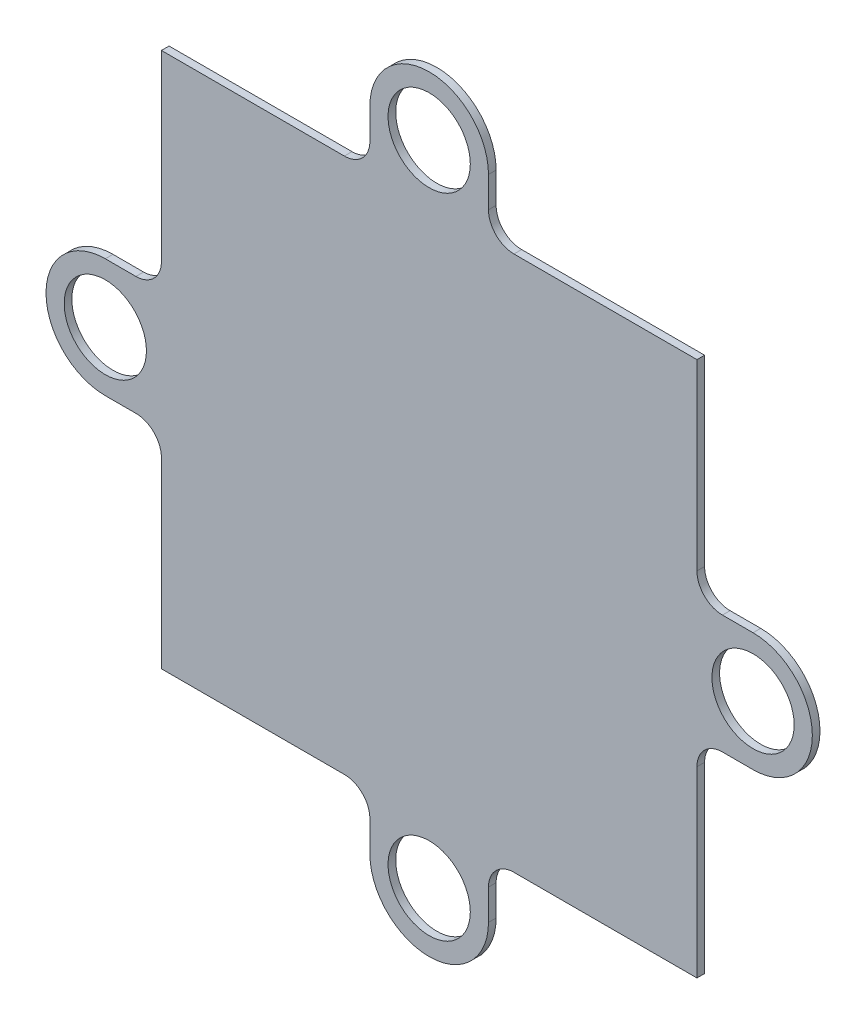
SolidWorks part; units mm, degrees
ref_plane "Front Plane" through (0, 0, 0) normal (0, 0, 1) x (1, 0, 0)
ref_plane "Top Plane" through (0, 0, 0) normal (0, 1, 0) x (1, 0, 0)
ref_plane "Right Plane" through (0, 0, 0) normal (1, 0, 0) x (0, 0, -1)
sketch "Sketch1" plane through (0, 0, 0) normal (0, 0, 1) x (1, 0, 0)
  line L0 (-4.65, 25.4) -> (-4.65, 23)
  line L1 (-21, -21) -> (-6.65, -21)
  line L2 (-21, -21) -> (-21, -6.65)
  line L3 (-21, 21) -> (-6.65, 21)
  line L4 (21, -21) -> (21, -6.65)
  line L5 (-21, -21) -> (21, 21) construction
  line L6 (-21, 21) -> (21, -21) construction
  line L7 (-6.65, 21) -> (-8.7591, 21)
  line L8 (4.65, 25.4) -> (4.65, 23)
  line L9 (6.65, 21) -> (7.1335, 21)
  line L10 (25.4, 4.65) -> (23, 4.65)
  line L11 (21, 6.65) -> (21, 8.7591)
  line L12 (25.4, -4.65) -> (23, -4.65)
  line L13 (21, -6.65) -> (21, -7.1335)
  line L14 (4.65, -25.4) -> (4.65, -23)
  line L15 (6.65, -21) -> (8.7591, -21)
  line L16 (-4.65, -25.4) -> (-4.65, -23)
  line L17 (-6.65, -21) -> (-7.1335, -21)
  line L18 (-25.4, -4.65) -> (-23, -4.65)
  line L19 (-21, -6.65) -> (-21, -8.7591)
  line L20 (-25.4, 4.65) -> (-23, 4.65)
  line L21 (-21, 6.65) -> (-21, 7.1335)
  line L22 (-21, 6.65) -> (-21, 21)
  line L23 (6.65, 21) -> (21, 21)
  line L24 (21, 6.65) -> (21, 21)
  line L25 (6.65, -21) -> (21, -21)
  circle A0 centre (0, 25.4) radius 3.225
  arc A1 (4.65, 25.4) -> (-4.65, 25.4) centre (0, 25.4) ccw
  arc A2 (4.65, 23) -> (6.65, 21) centre (6.65, 23) ccw
  arc A3 (-4.65, 23) -> (-6.65, 21) centre (-6.65, 23) cw
  circle A4 centre (25.4, 0) radius 3.225
  arc A5 (25.4, -4.65) -> (25.4, 4.65) centre (25.4, 0) ccw
  arc A6 (23, -4.65) -> (21, -6.65) centre (23, -6.65) ccw
  arc A7 (23, 4.65) -> (21, 6.65) centre (23, 6.65) cw
  circle A8 centre (0, -25.4) radius 3.225
  arc A9 (-4.65, -25.4) -> (4.65, -25.4) centre (0, -25.4) ccw
  arc A10 (-4.65, -23) -> (-6.65, -21) centre (-6.65, -23) ccw
  arc A11 (4.65, -23) -> (6.65, -21) centre (6.65, -23) cw
  circle A12 centre (-25.4, 0) radius 3.225
  arc A13 (-25.4, 4.65) -> (-25.4, -4.65) centre (-25.4, 0) ccw
  arc A14 (-23, 4.65) -> (-21, 6.65) centre (-23, 6.65) ccw
  arc A15 (-23, -4.65) -> (-21, -6.65) centre (-23, -6.65) cw
  point P0 (0, 0)
  point P53 (0, 0)
  dimension "D1" = 2
extrude "Boss-Extrude1" add sketch "Sketch1" along normal blind 0.6 contours L18 A15 L2 L1 A10 L16 A9 L14 A11 L15 L25 L4 A6 L12 A5 L10 A7 L11 L24 L23 L9 A2 L8 A1 L0 A3 L3 L22 L21 A14 L20 A13 A0 A4 A8 A12
